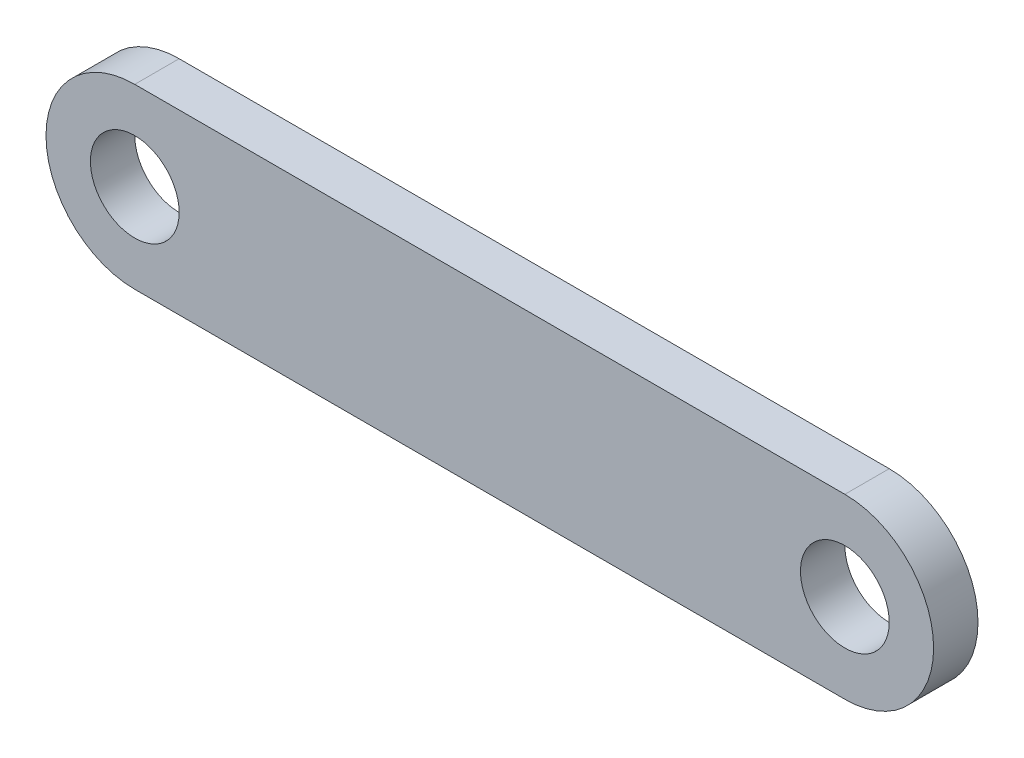
SolidWorks part; units mm, degrees
ref_plane "Front Plane" through (0, 0, 0) normal (0, 0, 1) x (1, 0, 0)
ref_plane "Top Plane" through (0, 0, 0) normal (0, 1, 0) x (1, 0, 0)
ref_plane "Right Plane" through (0, 0, 0) normal (1, 0, 0) x (0, 0, -1)
sketch "Sketch1" plane through (0, 0, 0) normal (0, 0, 1) x (1, 0, 0)
  line L0 (-25.4, 0) -> (25.4, 0) construction
  line L1 (-25.4, 6.35) -> (25.4, 6.35)
  line L2 (-25.4, -6.35) -> (25.4, -6.35)
  arc A0 (-25.4, 6.35) -> (-25.4, -6.35) centre (-25.4, 0) ccw
  arc A1 (25.4, -6.35) -> (25.4, 6.35) centre (25.4, 0) ccw
  circle A2 centre (-25.4, 0) radius 3.175
  circle A3 centre (25.4, 0) radius 3.175
  point P2 (0, 0)
  dimension "D3" = 6.35
  dimension "D1" = 12.7
  dimension "D2" = 50.8
extrude "Boss-Extrude2" add sketch "Sketch1" along normal blind 3.175 contours L2 A1 L1 A0 | A2 | A3
